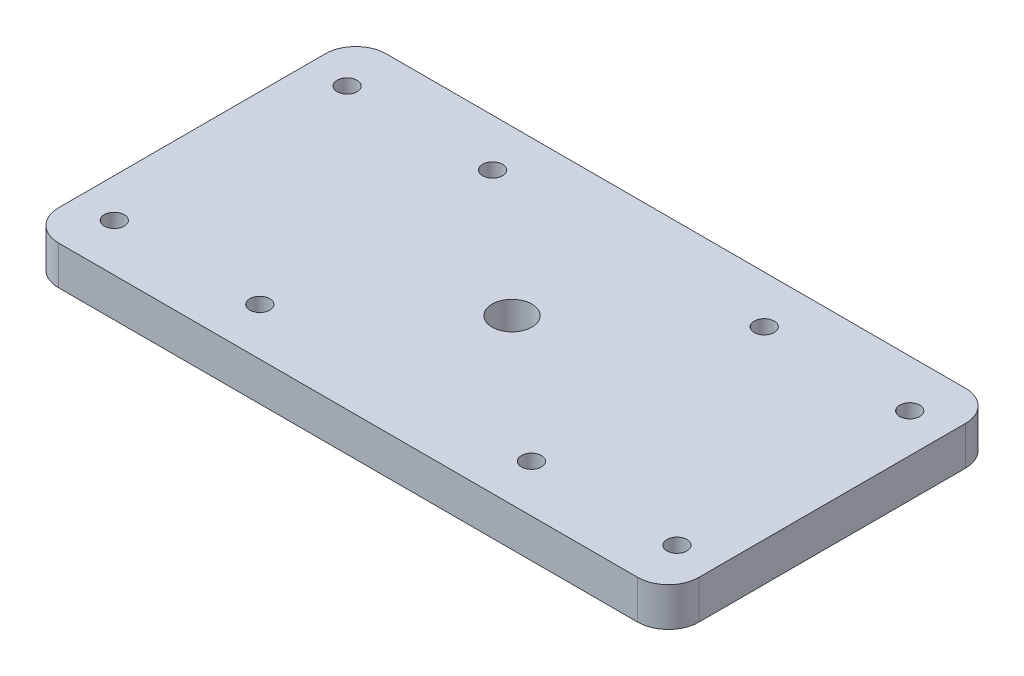
SolidWorks part; units mm, degrees
ref_plane "Front Plane" through (0, 0, 0) normal (0, 0, 1) x (1, 0, 0)
ref_plane "Top Plane" through (0, 0, 0) normal (0, 1, 0) x (1, 0, 0)
ref_plane "Right Plane" through (0, 0, 0) normal (1, 0, 0) x (0, 0, -1)
sketch "Sketch1" plane through (0, 0, 0) normal (0, 1, 0) x (1, 0, 0)
  line L1 (0, 53.63) -> (104.78, 53.63)
  line L2 (0, 53.63) -> (0, 0)
  line L3 (0, 0) -> (104.78, 0)
  line L4 (104.78, 53.63) -> (104.78, 0)
  dimension "D1" = 104.78
  dimension "D2" = 53.63
extrude "Boss-Extrude1" add sketch "Sketch1" along normal blind 6.35
sketch "Sketch2" plane through (0, 0, 0) normal (0, -1, 0) x (1, 0, 0)
  circle A0 centre (98.43, -45.865) radius 1.4224
  circle A1 centre (98.43, -45.865) radius 1.4224
  circle A2 centre (98.43, -7.765) radius 1.4224
  circle A3 centre (98.43, -7.765) radius 1.4224
  circle A4 centre (74.6175, -7.765) radius 1.4224
  circle A5 centre (74.6175, -7.765) radius 1.4224
  circle A6 centre (30.1675, -7.765) radius 1.4224
  circle A7 centre (30.1675, -7.765) radius 1.4224
  circle A8 centre (74.6175, -45.865) radius 1.4224
  circle A9 centre (74.6175, -45.865) radius 1.4224
  circle A10 centre (30.1675, -45.865) radius 1.4224
  circle A11 centre (30.1675, -45.865) radius 1.4224
  circle A12 centre (6.355, -45.865) radius 1.4224
  circle A13 centre (6.355, -45.865) radius 1.4224
  circle A14 centre (6.355, -7.765) radius 1.4224
  circle A15 centre (6.355, -7.765) radius 1.4224
hole_wizard "#30 (0.1285) Diameter Hole1" positions "Sketch3" profile "Sketch4" hole size "#30" standard "ANSI Inch" end condition through all
sketch "Sketch3" plane through (0, 0, 0) normal (0, -1, 0) x (-1, 0, 0)
  point P0 (-98.43, 7.765)
  point P3 (-98.43, 45.865)
  point P6 (-74.6175, 7.765)
  point P9 (-74.6175, 45.865)
  point P12 (-30.1675, 7.765)
  point P15 (-30.1675, 45.865)
  point P18 (-6.355, 7.765)
  point P21 (-6.355, 45.865)
sketch "Sketch4" plane through (98.43, 0, -7.765) normal (1, 0, 0) x (0, 0, -1)
  line L0 (0, 0) -> (0, 6.35)
  line L1 (0, 6.35) -> (1.6319, 6.35)
  line L2 (1.6319, 6.35) -> (1.6319, 0)
  line L5 (1.6319, 0) -> (0, 0)
  line L11 (0, -6.35) -> (0, 107.95) construction
  dimension "Thru Hole Dia." = 3.2639
  dimension "Thru Hole Depth" = 6.35
sketch "Sketch5" plane through (0, 0, 0) normal (0, -1, 0) x (1, 0, 0)
  line L0 (104.78, 0) -> (104.78, -53.63) construction
  line L2 (104.78, -53.63) -> (0, -53.63) construction
  point P0 (52.39, -26.815)
  dimension "D1" = 52.39
  dimension "D2" = 26.815
hole_wizard "F (0.257) Diameter Hole1" positions "Sketch6" profile "Sketch7" hole size "F" standard "ANSI Inch" end condition through all
sketch "Sketch6" plane through (0, 0, 0) normal (0, -1, 0) x (-1, 0, 0)
  point P0 (-52.39, 26.815)
sketch "Sketch7" plane through (52.39, 0, -26.815) normal (1, 0, 0) x (0, 0, -1)
  line L0 (0, 0) -> (0, 6.35)
  line L1 (0, 6.35) -> (3.2639, 6.35)
  line L2 (3.2639, 6.35) -> (3.2639, 0)
  line L5 (3.2639, 0) -> (0, 0)
  line L11 (0, -6.35) -> (0, 107.95) construction
  dimension "Thru Hole Dia." = 6.5278
  dimension "Thru Hole Depth" = 6.35
fillet "Fillet1" radius 5 4 edges at (0, 3.175, -53.63) (0, 3.175, 0) (104.78, 3.175, -53.63) (104.78, 3.175, 0)
